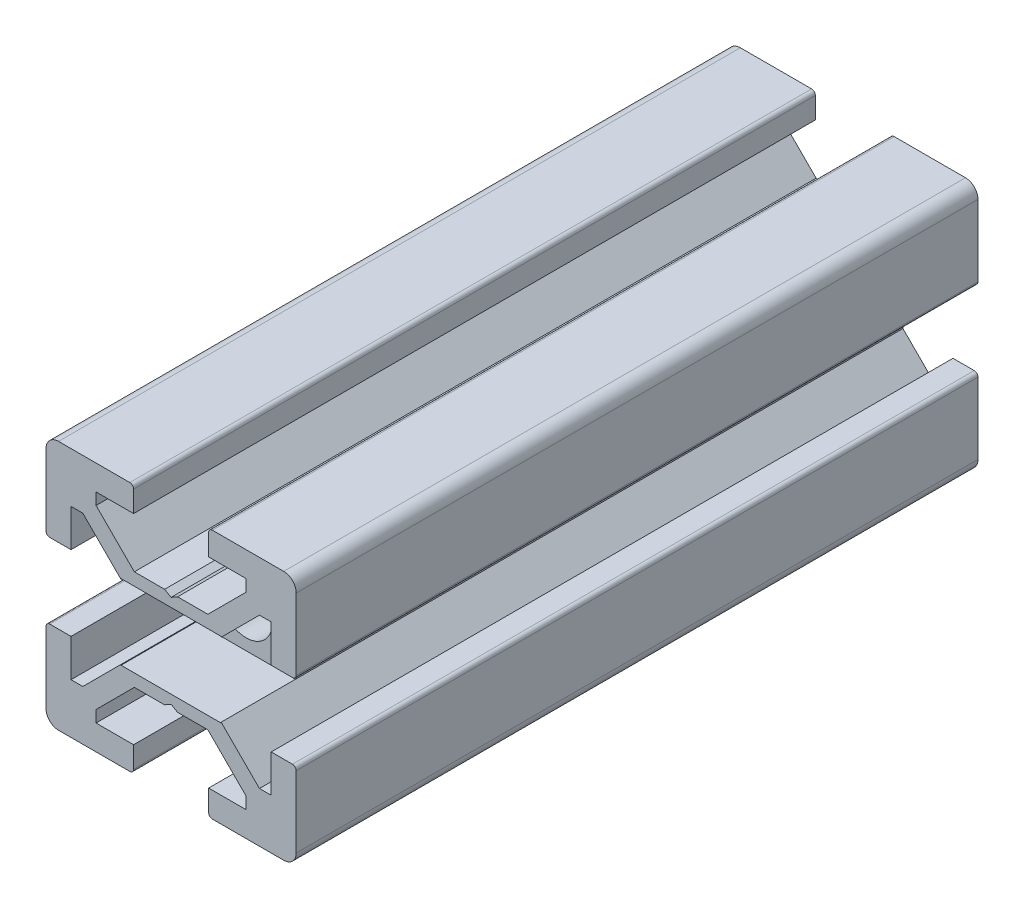
SolidWorks part; units mm, degrees
material "6063-T5"
ref_plane "Front Plane" through (0, 0, 0) normal (0, 0, 1) x (1, 0, 0)
ref_plane "Top Plane" through (0, 0, 0) normal (0, 1, 0) x (1, 0, 0)
ref_plane "Right Plane" through (0, 0, 0) normal (1, 0, 0) x (0, 0, -1)
ref_plane "Plane1" through (0, 0, 0) normal (0, 0, 1) x (1, 0, 0)
sketch "Sketch1" plane through (0, 0, 0) normal (0, 0, 1) x (1, 0, 0)
  line L0 (-10, 9) -> (-10, 3.3)
  line L1 (-9.7, 3) -> (-8, 3)
  line L2 (-8, 3) -> (-8, 6)
  line L3 (-8, 6) -> (-7.0607, 6)
  line L4 (-7.0607, 6) -> (-4, 2.9393)
  line L5 (-4, 2.9393) -> (-4, 0.5196)
  line L6 (-4, 0.5196) -> (-3.7, 0)
  line L7 (-3.7, 0) -> (-4, -0.5196)
  line L8 (-4, -0.5196) -> (-4, -2.9393)
  line L9 (-4, -2.9393) -> (-7.0607, -6)
  line L10 (-7.0607, -6) -> (-8, -6)
  line L11 (-8, -6) -> (-8, -3)
  line L12 (-8, -3) -> (-9.7, -3)
  line L13 (-10, -3.3) -> (-10, -9)
  line L14 (-9, -10) -> (-3.3, -10)
  line L15 (-3, -9.7) -> (-3, -8)
  line L16 (-3, -8) -> (-6, -8)
  line L17 (-6, -8) -> (-6, -7.0607)
  line L18 (-6, -7.0607) -> (-2.9393, -4)
  line L19 (-2.9393, -4) -> (-0.5196, -4)
  line L20 (-0.5196, -4) -> (0, -3.7)
  line L21 (0, -3.7) -> (0.5196, -4)
  line L22 (0.5196, -4) -> (2.9393, -4)
  line L23 (2.9393, -4) -> (6, -7.0607)
  line L24 (6, -7.0607) -> (6, -8)
  line L25 (6, -8) -> (3, -8)
  line L26 (3, -8) -> (3, -9.7)
  line L27 (3.3, -10) -> (9, -10)
  line L28 (10, -9) -> (10, -3.3)
  line L29 (9.7, -3) -> (8, -3)
  line L30 (8, -3) -> (8, -6)
  line L31 (8, -6) -> (7.0606, -6)
  line L32 (7.0606, -6) -> (4, -2.9393)
  line L33 (4, -2.9393) -> (4, -0.5196)
  line L34 (4, -0.5196) -> (3.7, 0)
  line L35 (3.7, 0) -> (4, 0.5196)
  line L36 (4, 0.5196) -> (4, 2.9393)
  line L37 (4, 2.9393) -> (7.0607, 6)
  line L38 (7.0607, 6) -> (8, 6)
  line L39 (8, 6) -> (8, 3)
  line L40 (8, 3) -> (9.7, 3)
  line L41 (10, 3.3) -> (10, 9)
  line L42 (9, 10) -> (3.3, 10)
  line L43 (3, 9.7) -> (3, 8)
  line L44 (3, 8) -> (6, 8)
  line L45 (6, 8) -> (6, 7.0607)
  line L46 (6, 7.0607) -> (2.9393, 4)
  line L47 (2.9393, 4) -> (0.5196, 4)
  line L48 (0.5196, 4) -> (0, 3.7)
  line L49 (0, 3.7) -> (-0.5196, 4)
  line L50 (-0.5196, 4) -> (-2.9394, 4)
  line L51 (-2.9394, 4) -> (-6, 7.0606)
  line L52 (-6, 7.0606) -> (-6, 8)
  line L53 (-6, 8) -> (-3, 8)
  line L54 (-3, 8) -> (-3, 9.7)
  line L55 (-3.3, 10) -> (-9, 10)
  arc A0 (-10, 3.3) -> (-9.7, 3) centre (-9.7, 3.3) ccw
  arc A1 (-9.7, -3) -> (-10, -3.3) centre (-9.7, -3.3) ccw
  arc A2 (-10, -9) -> (-9, -10) centre (-9, -9) ccw
  arc A3 (-3.3, -10) -> (-3, -9.7) centre (-3.3, -9.7) ccw
  arc A4 (3, -9.7) -> (3.3, -10) centre (3.3, -9.7) ccw
  arc A5 (9, -10) -> (10, -9) centre (9, -9) ccw
  arc A6 (10, -3.3) -> (9.7, -3) centre (9.7, -3.3) ccw
  arc A7 (9.7, 3) -> (10, 3.3) centre (9.7, 3.3) ccw
  arc A8 (10, 9) -> (9, 10) centre (9, 9) ccw
  arc A9 (3.3, 10) -> (3, 9.7) centre (3.3, 9.7) ccw
  arc A10 (-3, 9.7) -> (-3.3, 10) centre (-3.3, 9.7) ccw
  arc A11 (-9, 10) -> (-10, 9) centre (-9, 9) ccw
extrude "Boss-Extrude1" add sketch "Sketch1" against normal blind 54.5
ref_plane "Plane2" through (0, 0, 0) normal (1, 0, 0) x (0, 0, -1)
sketch "Sketch2" plane through (0, 0, 0) normal (1, 0, 0) x (0, 0, -1)
  line L0 (0, 0) -> (0, 2.1)
  line L1 (0, 2.1) -> (54.5, 2.1)
  line L2 (54.5, 2.1) -> (54.5, 0)
  line L3 (54.5, 0) -> (0, 0)
  line L4 (54.5, 0) -> (0, 0) construction
  dimension "D1" = 2.1
  dimension "D2" = 54.5
revolve "Cut-Revolve1" cut sketch "Sketch2" angle 360 about L4
ref_plane "Plane3" through (0, 0, -27.25) normal (0, 0, 1) x (1, 0, 0)
sketch "Sketch4" plane through (4, 0, 0) normal (1, 0, 0) x (0, 0, -1)
  line L0 (54.5, 0) -> (0, 0) construction
  line L1 (0, -2.9393) -> (0, -0.5196) construction
  line L2 (27.25, 2.9393) -> (27.25, -2.9393) construction
  line L3 (54.5, 2.9393) -> (0, 2.9393) construction
  line L4 (54.5, -2.9393) -> (0, -2.9393) construction
  circle A0 centre (10, 0) radius 2.5
  dimension "D1" = 5
  dimension "D2" = 10
extrude "Cut-Extrude1" cut sketch "Sketch4" against normal up to surface (8 mm away) up to face at (-4, 1.7295, -27.25)
sketch "Sketch5" plane through (4, 0, 0) normal (1, 0, 0) x (0, 0, -1)
  line L0 (6, -3) -> (0, -3)
  line L1 (6, -3) -> (6, 3)
  line L2 (0, -3) -> (0, 3)
  line L3 (6, 3) -> (0, 3)
  line L4 (6, -3) -> (0, 3) construction
  line L5 (0, -3) -> (6, 3) construction
  line L6 (54.5, 3) -> (0, 3) construction
  line L7 (7.5, 0) -> (0, 0) construction
  point P1 (3, 0)
  dimension "D1" = 6
extrude "Cut-Extrude2" cut sketch "Sketch5" against normal up to surface (8 mm away) up to face at (-4, 1.6563, -21.5)
